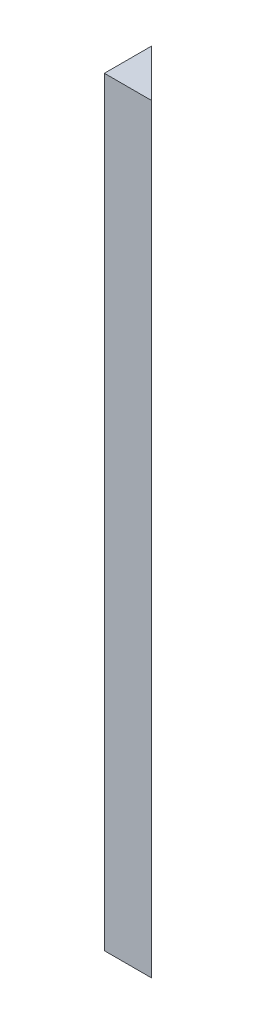
SolidWorks part; units mm, degrees
ref_plane "Front Plane" through (0, 0, 0) normal (0, 0, 1) x (1, 0, 0)
ref_plane "Top Plane" through (0, 0, 0) normal (0, 1, 0) x (1, 0, 0)
ref_plane "Right Plane" through (0, 0, 0) normal (1, 0, 0) x (0, 0, -1)
sketch "Sketch2" plane through (0, 0, 0) normal (0, 1, 0) x (1, 0, 0)
  line L0 (0, 0) -> (11.31, 0)
  line L1 (11.31, 0) -> (0, 11.31)
  line L2 (0, 11.31) -> (0, 0)
  dimension "D1" = 11.31
extrude "Boss-Extrude1" add sketch "Sketch2" along normal blind 182
